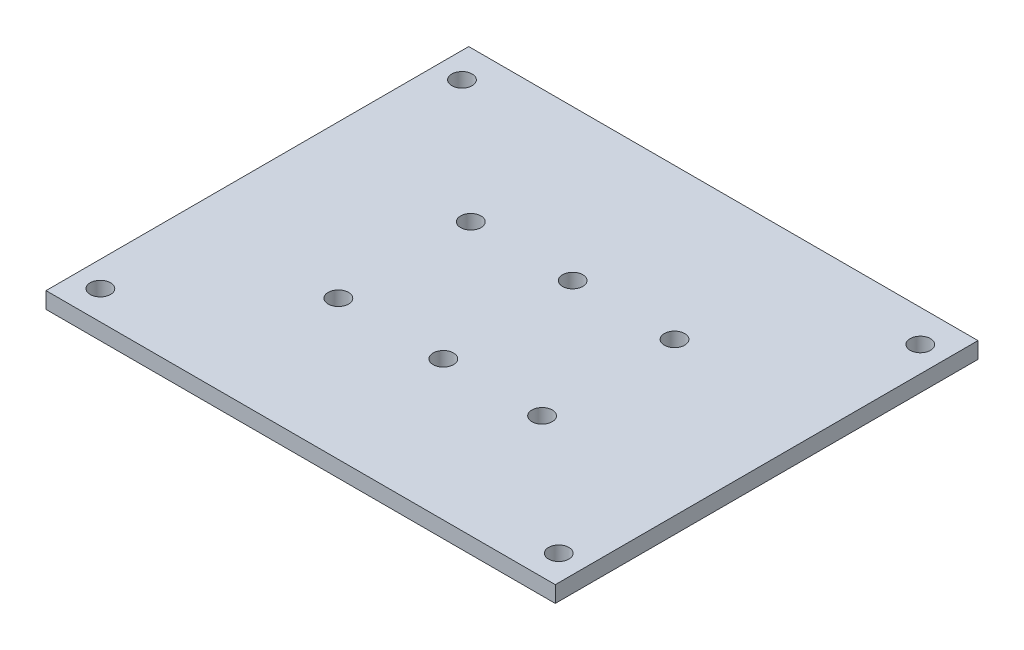
SolidWorks part; units mm, degrees
ref_plane "前视基准面" through (0, 0, 0) normal (0, 0, 1) x (1, 0, 0)
ref_plane "上视基准面" through (0, 0, 0) normal (0, 1, 0) x (1, 0, 0)
ref_plane "右视基准面" through (0, 0, 0) normal (1, 0, 0) x (0, 0, -1)
sketch "草图1" plane through (0, 0, 0) normal (0, 1, 0) x (1, 0, 0)
  line L1 (-30, 25.3652) -> (70, 25.3652)
  line L2 (-30, 25.3652) -> (-30, -57.6348)
  line L3 (-30, -57.6348) -> (70, -57.6348)
  line L4 (70, 25.3652) -> (70, -57.6348)
  circle A0 centre (-25, 19.0402) radius 2
  circle A1 centre (-25, -51.9598) radius 2
  circle A2 centre (65, -51.9598) radius 2
  circle A3 centre (65, 19.0402) radius 2
  circle A4 centre (20, -4.2257) radius 2
  circle A5 centre (20.6058, -30.2257) radius 2
  circle A6 centre (0, -30.2257) radius 2
  circle A7 centre (0, -4.2257) radius 2
  circle A8 centre (40, -4.2257) radius 2
  circle A9 centre (40, -30.2257) radius 2
  point P12 (0, 0)
  point P13 (-20.5081, -35.5373)
  point P14 (36.4617, -37.0196)
  point P15 (0, 0)
  point P16 (0, 0)
  point P17 (59.2337, 18.8209)
  point P18 (0, 0)
  point P19 (0, 0)
  point P20 (-25.3896, 19.0402)
  point P23 (-0.8713, -4.4284)
  point P24 (20.6058, 1.2495)
  point P27 (20.6058, -30.2257)
  point P30 (-2.476, 1.2495)
  point P33 (-0.1308, -30.2257)
  point P36 (42.2064, 1.2495)
  point P39 (42.2064, -30.2257)
  point P40 (-1.2416, 1.2495)
  point P41 (42.2064, -5.2924)
  point P42 (20.6058, -4.2257)
  point P43 (0, 0)
  point P44 (42.2064, -4.2257)
  point P45 (0, 0)
  point P46 (0, 0)
  point P47 (0, 0)
  point P48 (0, 0)
  point P49 (0, 0)
  point P50 (0, 0)
  point P51 (0, 0)
  point P52 (0, 0)
  point P53 (0, 0)
  point P54 (0, 0)
  dimension "D3" = 90
  dimension "D1" = 100
  dimension "D2" = 83
  dimension "D4" = 71
  dimension "D5" = 5
  dimension "D6" = 5
  dimension "D7" = 26
  dimension "D8" = 50
  dimension "D9" = 20
  dimension "D10" = 20
extrude "凸台-拉伸1" add sketch "草图1" along normal blind 3.2
